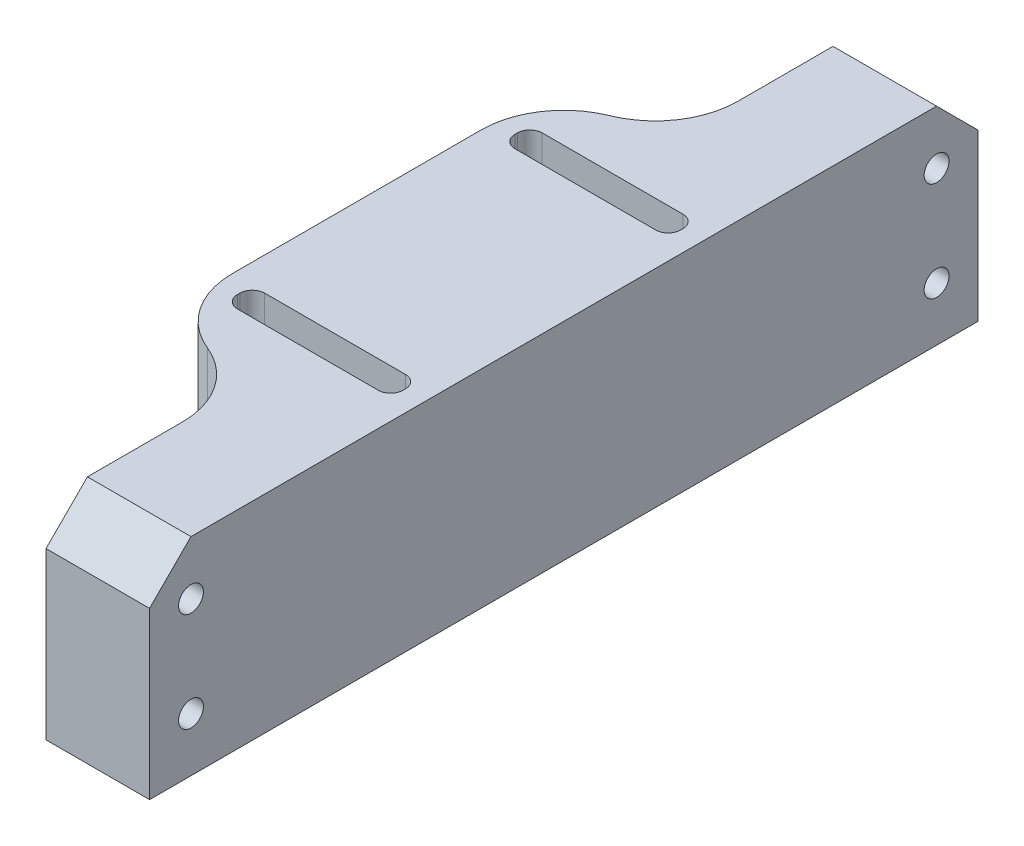
SolidWorks part; units mm, degrees
ref_plane "Спереди" through (0, 0, 0) normal (0, 0, 1) x (1, 0, 0)
ref_plane "Сверху" through (0, 0, 0) normal (0, 1, 0) x (1, 0, 0)
ref_plane "Справа" through (0, 0, 0) normal (1, 0, 0) x (0, 0, -1)
sketch "Эскиз1" plane through (0, 0, 0) normal (0, 1, 0) x (1, 0, 0)
  line L0 (-12.5, 16.75) -> (12.5, 16.75) construction
  line L1 (-12.5, -25) -> (0, -25)
  line L2 (0, -25) -> (0, -50)
  line L3 (0, -50) -> (12.5, -50)
  line L4 (-12.5, -25) -> (-12.5, 25)
  line L5 (12.5, -25) -> (-12.5, 25) construction
  line L6 (12.5, 25) -> (-12.5, -25) construction
  line L7 (-12.5, -16.75) -> (12.5, -16.75) construction
  line L8 (0, 25) -> (0, -25) construction
  line L9 (10, 15.1) -> (-10, 15.1)
  line L10 (10, 15.1) -> (10, 18.4)
  line L11 (10, 18.4) -> (-10, 18.4)
  line L12 (-10, 15.1) -> (-10, 18.4)
  line L13 (10, 15.1) -> (-10, 18.4) construction
  line L14 (10, 18.4) -> (-10, 15.1) construction
  line L15 (10, -18.4) -> (-10, -18.4)
  line L16 (10, -18.4) -> (10, -15.1)
  line L17 (10, -15.1) -> (-10, -15.1)
  line L18 (-10, -18.4) -> (-10, -15.1)
  line L19 (10, -18.4) -> (-10, -15.1) construction
  line L20 (10, -15.1) -> (-10, -18.4) construction
  line L21 (-10, 18.4) -> (10, -18.4) construction
  line L22 (-10, -18.4) -> (10, 18.4) construction
  line L23 (0, 25) -> (0, 50)
  line L24 (0, 50) -> (12.5, 50)
  line L25 (12.5, -50) -> (12.5, 50)
  line L26 (0, 25) -> (-12.5, 25)
  line L27 (12.5, 25) -> (-12.5, 25) construction
  line L28 (-12.5, -25) -> (12.5, -25) construction
  point P0 (0, 0)
  point P10 (0, 16.75)
  point P15 (0, -16.75)
  point P23 (0, 0)
  dimension "D1" = 3.3
  dimension "D2" = 20
  dimension "D3" = 25
  dimension "D4" = 33.5
  dimension "D5" = 50
  dimension "D6" = 100
extrude "Бобышка-Вытянуть1" add sketch "Эскиз1" along normal blind 25
sketch "Эскиз2" plane through (0, 0, 0) normal (-1, 0, 0) x (0, 0, 1)
  line L0 (-45, 0) -> (-45, 25) construction
  line L2 (-50, 0) -> (-25, 0) construction
  line L3 (-50, 25) -> (-25, 25) construction
  circle A0 centre (-45, 6.5) radius 1.5
  circle A1 centre (-45, 18.5) radius 1.5
  point P11 (-45, 12.5)
  dimension "D1" = 12
  dimension "D3" = 3
  dimension "D2" = 6
  dimension "D4" = 5
extrude "Вырез-Вытянуть1" cut sketch "Эскиз2" against normal through all
sketch "Эскиз3" plane through (0, 0, 0) normal (-1, 0, 0) x (0, 0, 1)
  line L0 (45, 0) -> (45, 25) construction
  line L3 (25, 0) -> (50, 0) construction
  line L4 (25, 25) -> (50, 25) construction
  circle A0 centre (45, 6.5) radius 1.5
  circle A1 centre (45, 18.5) radius 1.5
  point P10 (45, 12.5)
  dimension "D3" = 3
  dimension "D1" = 12
  dimension "D2" = 6
  dimension "D4" = 5
extrude "Вырез-Вытянуть2" cut sketch "Эскиз3" against normal through all
fillet "Скругление6" radius 10 2 edges at (-12.5, 12.5, 25) (-12.5, 12.5, -25)
fillet "Скругление7" radius 1.5 8 edges at (-10, 12.5, 18.4) (-10, 12.5, 15.1) (10, 12.5, 15.1) (10, 12.5, 18.4) (10, 12.5, -15.1) (10, 12.5, -18.4) (-10, 12.5, -15.1) (-10, 12.5, -18.4)
chamfer "Фаска1" distance 5 angle 45 2 edges at (6.25, 25, 50) (6.25, 25, -50)
fillet "Скругление8" radius 10 2 edges at (0, 12.5, 25) (0, 12.5, -25)
